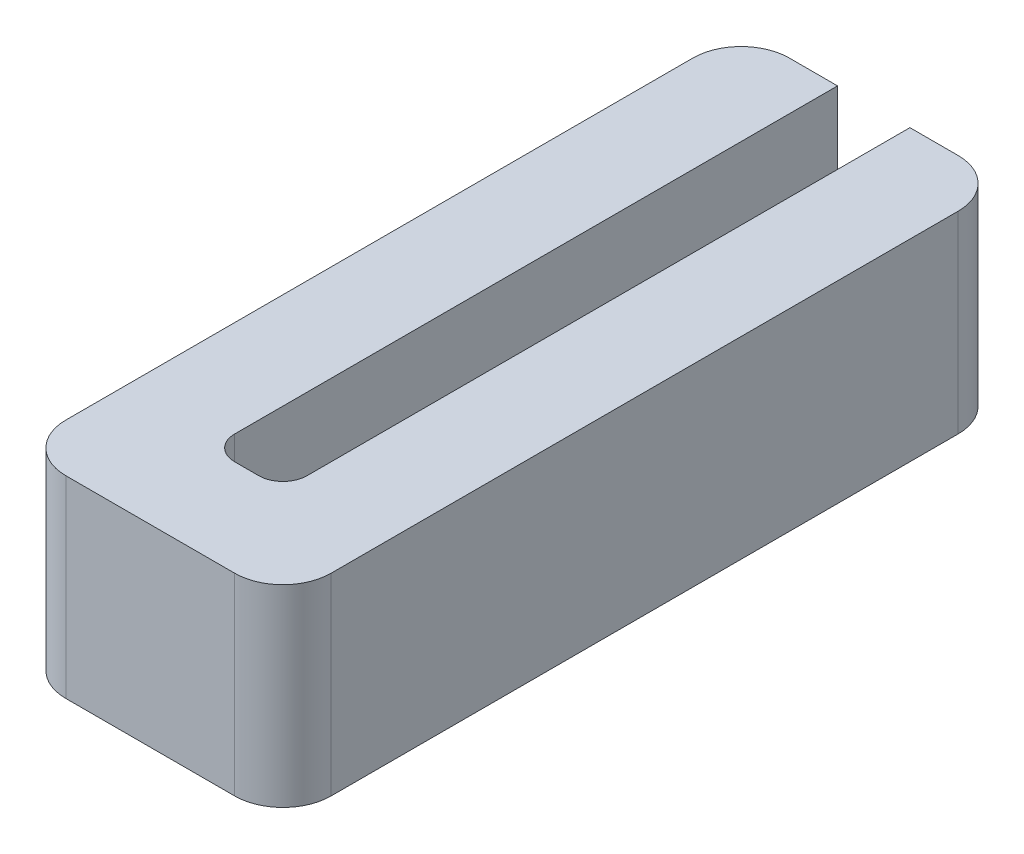
SolidWorks part; units mm, degrees
ref_plane "Alzado" through (0, 0, 0) normal (0, 0, 1) x (1, 0, 0)
ref_plane "Planta" through (0, 0, 0) normal (0, 1, 0) x (1, 0, 0)
ref_plane "Vista lateral" through (0, 0, 0) normal (1, 0, 0) x (0, 0, -1)
sketch "Croquis1" plane through (0, 0, 0) normal (0, 1, 0) x (1, 0, 0)
  line L0 (3.5, 0) -> (5.5, 0)
  line L1 (0, 0) -> (2, 0)
  line L2 (0, 0) -> (0, -15)
  line L3 (0, -15) -> (5.5, -15)
  line L4 (5.5, 0) -> (5.5, -15)
  line L6 (2, 0) -> (2, -13)
  line L7 (2, -13) -> (3.5, -13)
  line L8 (3.5, 0) -> (3.5, -13)
  dimension "D1" = 5.5
  dimension "D2" = 15
  dimension "D3" = 13
  dimension "D4" = 1.5
  dimension "D5" = 2
extrude "Saliente-Extruir1" add sketch "Croquis1" along normal blind 4
fillet "Redondeo1" radius 1 4 edges at (0, 2, 0) (5.5, 2, 0) (5.5, 2, 15) (0, 2, 15)
fillet "Redondeo2" radius 0.5 2 edges at (3.5, 2, 13) (2, 2, 13)
